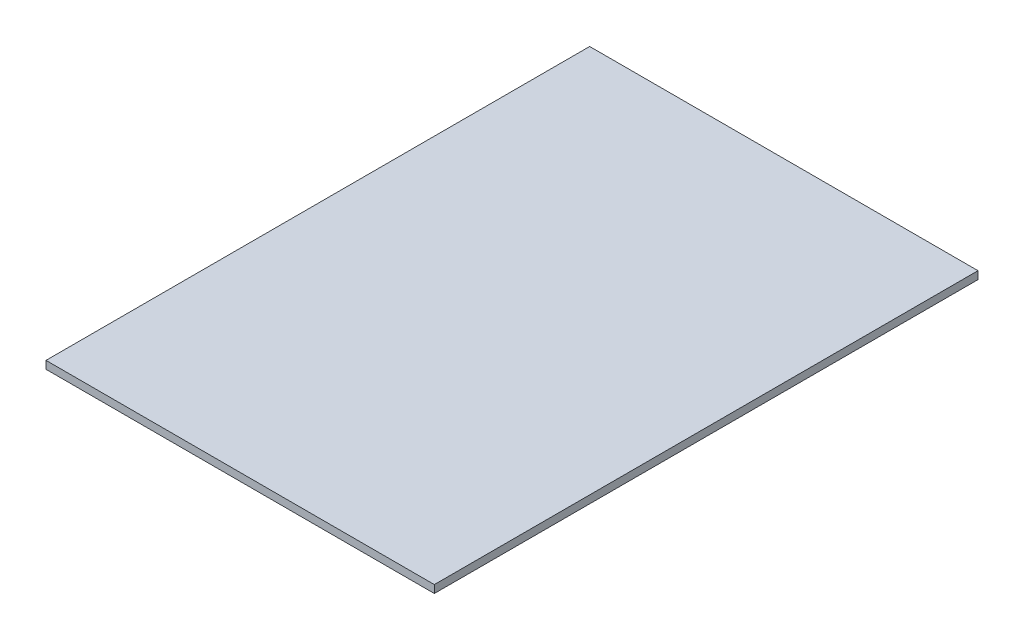
SolidWorks part; units mm, degrees
material "ABS"
ref_plane "Front Plane" through (0, 0, 0) normal (0, 0, 1) x (1, 0, 0)
ref_plane "Top Plane" through (0, 0, 0) normal (0, 1, 0) x (1, 0, 0)
ref_plane "Right Plane" through (0, 0, 0) normal (1, 0, 0) x (0, 0, -1)
sketch "Sketch2" plane through (0, 0, 0) normal (0, 1, 0) x (1, 0, 0)
  line L1 (0, 0) -> (250, 0)
  line L2 (0, 0) -> (0, 350)
  line L3 (0, 350) -> (250, 350)
  line L4 (250, 0) -> (250, 350)
  dimension "D1" = 250
  dimension "D2" = 350
extrude "Boss-Extrude1" add sketch "Sketch2" along normal blind 5
